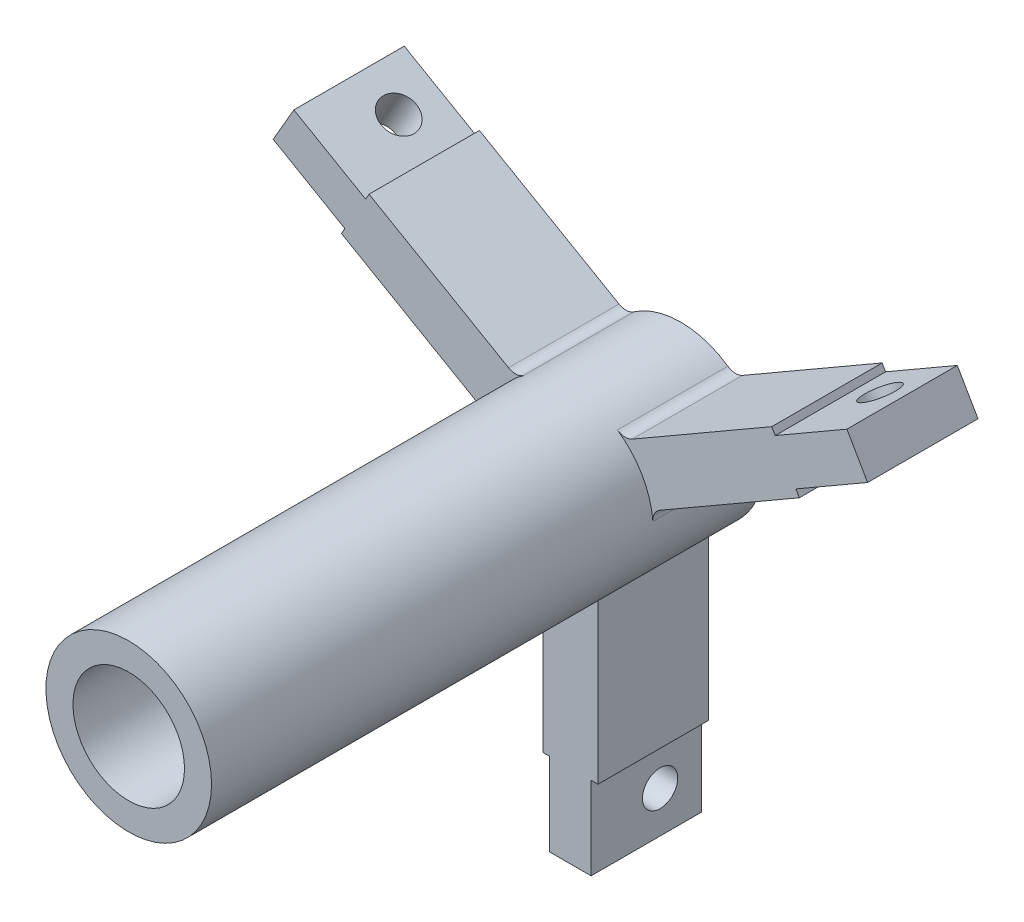
SolidWorks part; units mm, degrees
ref_plane "Plane1" through (0, 0, 0) normal (0, 0, 1) x (1, 0, 0)
ref_plane "Plane2" through (0, 0, 0) normal (0, 1, 0) x (1, 0, 0)
ref_plane "Plane3" through (0, 0, 0) normal (1, 0, 0) x (0, 0, -1)
other "Configuration Table"
sketch "Sketch1" plane through (0, 0, 0) normal (0, 0, 1) x (1, 0, 0)
  circle A0 centre (0, 0) radius 12.827
  circle A1 centre (0, 0) radius 19.05
  dimension "D1" = 25.654
  dimension "D2" = 38.1
extrude "Base-Extrude" add sketch "Sketch1" along normal blind 127
ref_plane "Plane4" through (0, -76.2, 0) normal (0, 1, 0) x (-1, 0, 0)
sketch "Sketch2" plane through (0, -76.2, 0) normal (0, 1, 0) x (-1, 0, 0)
  line L0 (0, 0) -> (0, 23.9235) construction
  line L1 (4.7625, 0) -> (-4.7625, 0)
  line L2 (-19.05, 0) -> (19.05, 0) construction
  line L3 (-4.7625, 0) -> (-4.7625, 25.4)
  line L4 (4.7625, 0) -> (4.7625, 25.4)
  line L5 (-4.7625, 25.4) -> (4.7625, 25.4)
  point P7 (0, 0)
  point P11 (0, 25.4)
  dimension "D1" = 25.4
  dimension "D2" = 9.525
extrude "Boss-Extrude1" add sketch "Sketch2" along normal up to surface (57.7549 mm away)
sketch "Sketch3" plane through (-4.7625, 0, 0) normal (-1, 0, 0) x (0, 0, 1)
  line L0 (0, -76.2) -> (25.4, -76.2) construction
  line L1 (0, -18.4451) -> (0, -76.2) construction
  circle A0 centre (9.525, -66.675) radius 4.064
  dimension "D1" = 8.128
  dimension "D2" = 9.525
  dimension "D3" = 9.525
extrude "Cut-Extrude1" cut sketch "Sketch3" against normal through all
pattern_circular "CirPattern1" count 3 every 120 about axis through (0, 0, 0) along (0, 0, 1) of "Boss-Extrude1"
sketch "Sketch6" plane through (-45.6189, 20.8388, 50.9368) normal (-0.5, -0.866, 0) x (0.866, -0.5, 0)
  line L0 (-26.2735, -50.9368) -> (-26.2735, -25.5368) construction
  line L1 (31.4814, -50.9368) -> (-26.2735, -50.9368) construction
  circle A0 centre (-16.7485, -41.4118) radius 4.064
  dimension "D1" = 8.128
  dimension "D2" = 9.525
  dimension "D3" = 9.525
extrude "Cut-Extrude2" cut sketch "Sketch6" against normal through all
sketch "Sketch7" plane through (34.3776, 14.3486, 49.693) normal (0.5, -0.866, 0) x (0.866, 0.5, 0)
  line L0 (39.2538, -49.693) -> (39.2538, -24.293) construction
  line L1 (-18.5011, -49.693) -> (39.2538, -49.693) construction
  circle A0 centre (29.7288, -40.168) radius 4.064
  dimension "D1" = 8.128
  dimension "D2" = 9.525
  dimension "D3" = 9.525
extrude "Cut-Extrude3" cut sketch "Sketch7" against normal through all
ref_plane "Plane5" through (0, 15.875, 0) normal (0, 1, 0) x (-1, 0, 0)
sketch "Sketch10" plane through (0, 15.875, 0) normal (0, 1, 0) x (-1, 0, 0)
  line L0 (0, 0) -> (0, 58.2673) construction
  line L2 (-12.827, 0) -> (12.827, 0) construction
  circle A0 centre (0, 38.1) radius 7.1501
  dimension "D1" = 14.3002
  dimension "D2" = 38.1
extrude "Cut-Extrude4" cut sketch "Sketch10" against normal blind 0.635
hole_wizard "Hole2" positions "Sketch11" profile "Sketch12" legacy
sketch "Sketch11" plane through (0, 15.24, 0) normal (0, 1, 0) x (-1, 0, 0)
  point P0 (0, 38.1)
sketch "Sketch12" plane through (0, 15.24, 38.1) normal (1, 0, 0) x (0, 0, 1)
  line L0 (0, 0) -> (0, 14.2338)
  line L1 (0, 14.2338) -> (2.5527, 12.7)
  line L2 (2.5527, 12.7) -> (2.5527, 9.525)
  line L3 (2.5527, 9.525) -> (3.175, 9.525)
  line L4 (3.175, 9.525) -> (3.175, 0.0025)
  line L5 (3.175, 0.0025) -> (3.175, 0)
  line L6 (3.175, 0) -> (0, 0)
ref_plane "Plane6" through (0, -57.15, 0) normal (0, 1, 0) x (-1, 0, 0)
sketch "Sketch13" plane through (0, -57.15, 0) normal (0, 1, 0) x (-1, 0, 0)
  line L0 (0, 25.4) -> (0, -5.2456) construction
  line L1 (-4.7625, 25.4) -> (4.7625, 25.4) construction
  line L2 (6.35, 25.4) -> (-6.35, 25.4)
  line L3 (-6.35, 25.4) -> (-6.35, 0)
  line L4 (6.35, 25.4) -> (6.35, 0)
  line L5 (-6.35, 0) -> (6.35, 0)
  point P8 (0, 25.4)
  point P9 (0, 25.4)
  point P12 (0, 0)
  dimension "D1" = 12.7
extrude "Boss-Extrude3" add sketch "Sketch13" along normal up to surface (39.1895 mm away)
pattern_circular "CirPattern2" count 3 every 120 about axis through (0, 0, 0) along (0, 0, 1) of "Boss-Extrude3"
fillet "Fillet1" radius 3.175 2 edges at (12.3793, 14.4795, 12.7) (-29.3488, 24.2769, 25.4)
fillet "Fillet2" radius 3.175 2 edges at (-18.7293, 3.481, 12.7) (-6.35, -17.9605, 12.7)
fillet "Fillet3" radius 3.175 2 edges at (18.7293, 3.481, 12.7) (6.35, -17.9605, 12.7)
